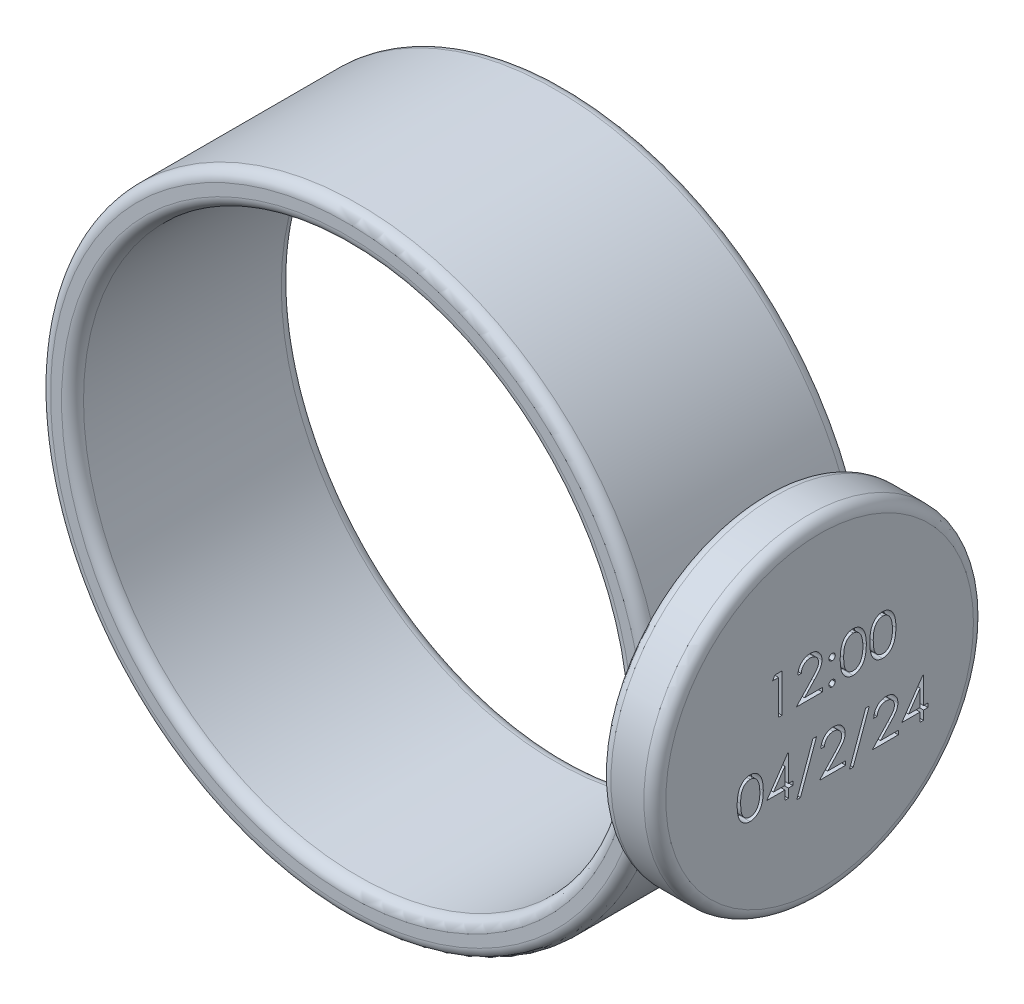
SolidWorks part; units mm, degrees
ref_plane "Front Plane" through (0, 0, 0) normal (0, 0, 1) x (1, 0, 0)
ref_plane "Top Plane" through (0, 0, 0) normal (0, 1, 0) x (1, 0, 0)
ref_plane "Right Plane" through (0, 0, 0) normal (1, 0, 0) x (0, 0, -1)
sketch "Sketch1" plane through (0, 0, 0) normal (0, 0, 1) x (1, 0, 0)
  circle A0 centre (0, 0) radius 25
  circle A1 centre (0, 0) radius 28
  dimension "D1" = 50
  dimension "D2" = 3
extrude "Boss-Extrude1" add sketch "Sketch1" along normal blind 20
ref_plane "Plane1" through (28, 0, 0) normal (1, 0, 0) x (0, 0, -1)
sketch "Sketch2" plane through (28, 0, 0) normal (1, 0, 0) x (0, 0, -1)
  line L0 (0, -28) -> (0, 28) construction
  line L3 (-20, 0) -> (0, 0) construction
  line L4 (-20, 28) -> (-20, -28) construction
  circle A0 centre (-10, 0) radius 15
  point P4 (0, 0)
  dimension "D2" = 30
  dimension "D1" = 10
extrude "Boss-Extrude2" add sketch "Sketch2" along normal blind 5 separate body
fillet "Fillet1" radius 1 2 edges at (28, 0, -5) (33, 0, -5)
fillet "Fillet5" radius 1 4 edges at (25, 0, 0) (28, 0, 0) (25, 0, 20) (28, 0, 20)
sketch "Sketch5" plane through (33, 0, 0) normal (1, 0, 0) x (0, 0, -1)
  text T0 "  12:00\r\n04/2/24"
extrude "Cut-Extrude3" cut sketch "Sketch5" against normal blind 1
